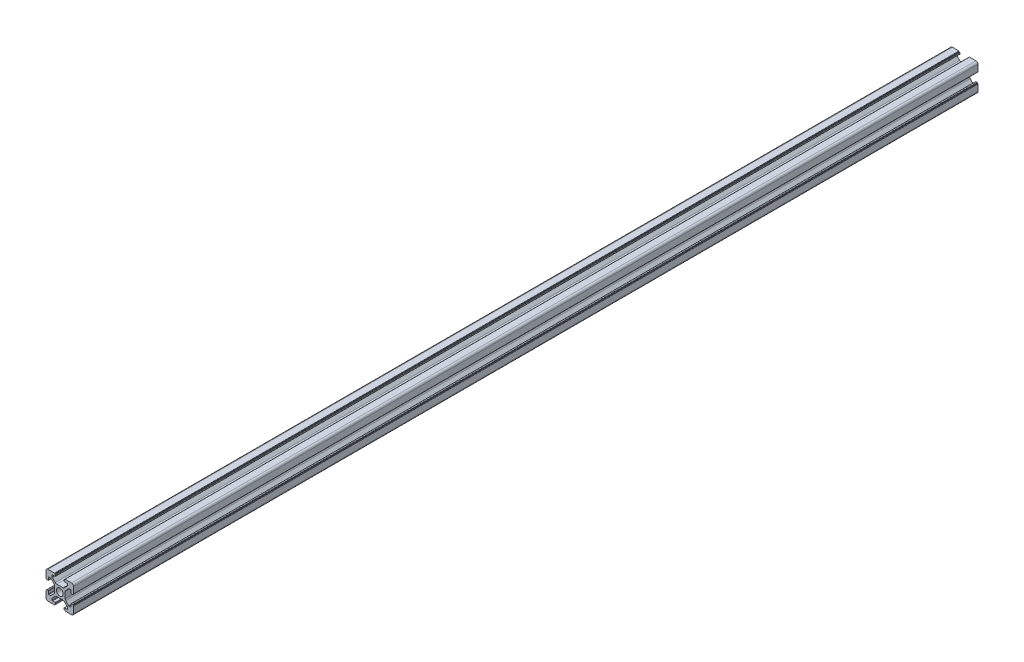
SolidWorks part; units mm, degrees
ref_plane "前视基准面" through (0, 0, 0) normal (0, 0, 1) x (1, 0, 0)
ref_plane "上视基准面" through (0, 0, 0) normal (0, 1, 0) x (1, 0, 0)
ref_plane "右视基准面" through (0, 0, 0) normal (1, 0, 0) x (0, 0, -1)
sketch "草图1" plane through (0, 0, 0) normal (0, 0, 1) x (1, 0, 0)
  line L0 (0, 0) -> (0, 5.5) construction
  line L1 (-8.5023, -10.0023) -> (-3.85, -10.0023)
  line L2 (-10.0023, -8.5023) -> (-10.0023, -3.85)
  line L3 (-8.5023, 10.0023) -> (-3.85, 10.0023)
  line L4 (10.0023, -8.5023) -> (10.0023, -3.85)
  line L5 (-10.0023, -10.0023) -> (10.0023, 10.0023) construction
  line L6 (-10.0023, 10.0023) -> (10.0023, -10.0023) construction
  line L7 (-2.218, -3.9) -> (2.218, -3.9)
  line L8 (-3.9, -2.218) -> (-3.9, 2.218)
  line L9 (-2.218, 3.9) -> (2.218, 3.9)
  line L10 (3.9, -2.218) -> (3.9, 2.218)
  line L11 (-3.9, -3.9) -> (3.9, 3.9) construction
  line L12 (-3.9, 3.9) -> (3.9, -3.9) construction
  line L13 (-5.25, -8.2) -> (-3.35, -8.2)
  line L14 (-8.2, -5.25) -> (-8.2, -3.35)
  line L15 (-5.25, 8.2) -> (-3.35, 8.2)
  line L16 (8.2, -5.25) -> (8.2, -3.35)
  line L17 (-8.2, -8.2) -> (8.2, 8.2) construction
  line L18 (-8.2, 8.2) -> (8.2, -8.2) construction
  line L19 (-7.95, 5.5) -> (-6.6642, 5.5)
  line L20 (0, 0) -> (5.5, 0) construction
  line L23 (-5.5, 7.95) -> (-5.5, 6.6642)
  line L26 (0, 0) -> (-0.5303, 0.5303)
  line L27 (3.2787, 4.3393) -> (5.4268, 6.4874)
  line L28 (0, 0) -> (0.5303, -0.5303)
  line L29 (5.5, 6.6642) -> (5.5, 7.95)
  line L30 (4.3393, 3.2787) -> (6.4874, 5.4268)
  line L31 (6.6642, 5.5) -> (7.95, 5.5)
  line L32 (4.3393, -3.2787) -> (6.4874, -5.4268)
  line L33 (3.2787, -4.3393) -> (5.4268, -6.4874)
  line L34 (-3.2787, -4.3393) -> (-5.4268, -6.4874)
  line L35 (-4.3393, -3.2787) -> (-6.4874, -5.4268)
  line L36 (-4.3393, 3.2787) -> (-6.4874, 5.4268)
  line L37 (-3.2787, 4.3393) -> (-5.4268, 6.4874)
  line L38 (3.1, -8.45) -> (3.1, -9.2523)
  line L39 (8.45, 3.1) -> (9.2523, 3.1)
  line L40 (-5.5, -6.6642) -> (-5.5, -7.95)
  line L41 (-6.6642, -5.5) -> (-7.95, -5.5)
  line L42 (5.5, -6.6642) -> (5.5, -7.95)
  line L43 (6.6642, -5.5) -> (7.95, -5.5)
  line L44 (9.2523, -3.1) -> (8.45, -3.1)
  line L46 (10.0023, 3.85) -> (10.0023, 8.5023)
  line L47 (8.2, 3.35) -> (8.2, 5.25)
  line L48 (-3.1, -9.2523) -> (-3.1, -8.45)
  line L49 (-8.45, -3.1) -> (-9.2523, -3.1)
  line L50 (-9.2523, 3.1) -> (-8.45, 3.1)
  line L51 (-3.1, 8.45) -> (-3.1, 9.2523)
  line L52 (3.1, 9.2523) -> (3.1, 8.45)
  line L53 (3.85, 10.0023) -> (8.5023, 10.0023)
  line L54 (3.35, 8.2) -> (5.25, 8.2)
  line L55 (-10.0023, 3.85) -> (-10.0023, 8.5023)
  line L56 (-8.2, 3.35) -> (-8.2, 5.25)
  line L57 (3.35, -8.2) -> (5.25, -8.2)
  line L58 (3.85, -10.0023) -> (8.5023, -10.0023)
  line L59 (9.7523, -3.6) -> (9.5023, -3.6)
  line L61 (9.7523, 3.6) -> (9.5023, 3.6)
  line L62 (9.5023, -3.6) -> (9.5023, -3.35)
  line L63 (3.6, -9.7523) -> (3.6, -9.5023)
  line L64 (3.35, -9.5023) -> (3.6, -9.5023)
  line L65 (9.5023, 3.35) -> (9.5023, 3.6)
  line L66 (-3.6, -9.5023) -> (-3.35, -9.5023)
  line L67 (-3.6, -9.7523) -> (-3.6, -9.5023)
  line L68 (-9.7523, -3.6) -> (-9.5023, -3.6)
  line L69 (-9.5023, -3.35) -> (-9.5023, -3.6)
  line L70 (-9.5023, 3.6) -> (-9.5023, 3.35)
  line L71 (-9.7523, 3.6) -> (-9.5023, 3.6)
  line L72 (-3.6, 9.7523) -> (-3.6, 9.5023)
  line L73 (-3.35, 9.5023) -> (-3.6, 9.5023)
  line L74 (3.6, 9.5023) -> (3.35, 9.5023)
  line L75 (3.6, 9.7523) -> (3.6, 9.5023)
  circle A0 centre (0, 0) radius 2.5
  arc A1 (10.0023, 8.5023) -> (8.5023, 10.0023) centre (8.5023, 8.5023) ccw
  arc A2 (8.5023, -10.0023) -> (10.0023, -8.5023) centre (8.5023, -8.5023) ccw
  arc A3 (-10.0023, -8.5023) -> (-8.5023, -10.0023) centre (-8.5023, -8.5023) ccw
  arc A4 (-10.0023, 8.5023) -> (-8.5023, 10.0023) centre (-8.5023, 8.5023) cw
  arc A5 (-9.5023, -3.35) -> (-9.2523, -3.1) centre (-9.2523, -3.35) cw
  arc A6 (-9.7523, -3.6) -> (-10.0023, -3.85) centre (-9.7523, -3.85) ccw
  arc A7 (-8.45, -3.1) -> (-8.2, -3.35) centre (-8.45, -3.35) cw
  arc A8 (-7.95, -5.5) -> (-8.2, -5.25) centre (-7.95, -5.25) cw
  arc A9 (-6.4874, -5.4268) -> (-6.6642, -5.5) centre (-6.6642, -5.25) cw
  arc A10 (-5.4268, -6.4874) -> (-5.5, -6.6642) centre (-5.25, -6.6642) ccw
  arc A11 (-5.5, -7.95) -> (-5.25, -8.2) centre (-5.25, -7.95) ccw
  arc A12 (-3.6, -9.7523) -> (-3.85, -10.0023) centre (-3.85, -9.7523) cw
  arc A13 (-3.35, -9.5023) -> (-3.1, -9.2523) centre (-3.35, -9.2523) ccw
  arc A14 (-3.1, -8.45) -> (-3.35, -8.2) centre (-3.35, -8.45) ccw
  arc A15 (3.1, -8.45) -> (3.35, -8.2) centre (3.35, -8.45) cw
  arc A16 (5.5, -7.95) -> (5.25, -8.2) centre (5.25, -7.95) cw
  arc A17 (5.4268, -6.4874) -> (5.5, -6.6642) centre (5.25, -6.6642) cw
  arc A18 (6.4874, -5.4268) -> (6.6642, -5.5) centre (6.6642, -5.25) ccw
  arc A19 (7.95, -5.5) -> (8.2, -5.25) centre (7.95, -5.25) ccw
  arc A20 (8.45, -3.1) -> (8.2, -3.35) centre (8.45, -3.35) ccw
  arc A21 (9.5023, -3.35) -> (9.2523, -3.1) centre (9.2523, -3.35) ccw
  arc A22 (9.7523, -3.6) -> (10.0023, -3.85) centre (9.7523, -3.85) cw
  arc A23 (3.35, -9.5023) -> (3.1, -9.2523) centre (3.35, -9.2523) cw
  arc A24 (3.6, -9.7523) -> (3.85, -10.0023) centre (3.85, -9.7523) ccw
  arc A25 (7.95, 5.5) -> (8.2, 5.25) centre (7.95, 5.25) cw
  arc A26 (8.2, 3.35) -> (8.45, 3.1) centre (8.45, 3.35) ccw
  arc A27 (9.5023, 3.35) -> (9.2523, 3.1) centre (9.2523, 3.35) cw
  arc A28 (9.7523, 3.6) -> (10.0023, 3.85) centre (9.7523, 3.85) ccw
  arc A29 (6.6642, 5.5) -> (6.4874, 5.4268) centre (6.6642, 5.25) ccw
  arc A30 (5.4268, 6.4874) -> (5.5, 6.6642) centre (5.25, 6.6642) ccw
  arc A31 (5.5, 7.95) -> (5.25, 8.2) centre (5.25, 7.95) ccw
  arc A32 (3.1, 8.45) -> (3.35, 8.2) centre (3.35, 8.45) ccw
  arc A33 (3.6, 9.7523) -> (3.85, 10.0023) centre (3.85, 9.7523) cw
  arc A34 (3.35, 9.5023) -> (3.1, 9.2523) centre (3.35, 9.2523) ccw
  arc A35 (-9.7523, 3.6) -> (-10.0023, 3.85) centre (-9.7523, 3.85) cw
  arc A36 (-9.5023, 3.35) -> (-9.2523, 3.1) centre (-9.2523, 3.35) ccw
  arc A37 (-8.45, 3.1) -> (-8.2, 3.35) centre (-8.45, 3.35) ccw
  arc A38 (-8.2, 5.25) -> (-7.95, 5.5) centre (-7.95, 5.25) cw
  arc A39 (-6.4874, 5.4268) -> (-6.6642, 5.5) centre (-6.6642, 5.25) ccw
  arc A40 (-5.4268, 6.4874) -> (-5.5, 6.6642) centre (-5.25, 6.6642) cw
  arc A41 (-5.5, 7.95) -> (-5.25, 8.2) centre (-5.25, 7.95) cw
  arc A42 (-3.1, 8.45) -> (-3.35, 8.2) centre (-3.35, 8.45) cw
  arc A43 (-3.1, 9.2523) -> (-3.35, 9.5023) centre (-3.35, 9.2523) ccw
  arc A44 (-3.6, 9.7523) -> (-3.85, 10.0023) centre (-3.85, 9.7523) ccw
  arc A45 (-4.3393, 3.2787) -> (-3.9, 2.218) centre (-5.4, 2.218) cw
  arc A46 (-3.2787, 4.3393) -> (-2.218, 3.9) centre (-2.218, 5.4) ccw
  arc A47 (3.2787, 4.3393) -> (2.218, 3.9) centre (2.218, 5.4) cw
  arc A48 (4.3393, 3.2787) -> (3.9, 2.218) centre (5.4, 2.218) ccw
  arc A49 (4.3393, -3.2787) -> (3.9, -2.218) centre (5.4, -2.218) cw
  arc A50 (3.2787, -4.3393) -> (2.218, -3.9) centre (2.218, -5.4) ccw
  arc A51 (-4.3393, -3.2787) -> (-3.9, -2.218) centre (-5.4, -2.218) ccw
  arc A52 (-2.218, -3.9) -> (-3.2787, -4.3393) centre (-2.218, -5.4) ccw
  point P0 (0, 0)
  point P7 (10.0023, 0)
  point P62 (0, 0)
  point P76 (0, 0)
  point P92 (-8.2, -5.5)
  point P99 (0, 0)
  point P106 (-5.5, -8.2)
  point P117 (5.5, -8.2)
  point P124 (8.2, -5.5)
  point P137 (8.2, 5.5)
  point P140 (8.2, 3.1)
  point P147 (6.5607, 5.5)
  point P152 (5.5, 8.2)
  point P167 (-8.2, 5.5)
  point P174 (-5.5, 8.2)
  dimension "D1" = 1.5
  dimension "D5" = 0.25
  dimension "D6" = 1.5
  dimension "D2" = 4
  dimension "D3" = 4
  dimension "D4" = 4
extrude "凸台-拉伸1" add sketch "草图1" along normal blind 1220 contours A52 L7 A50 L33 A17 L42 A16 L57 A15 L38 A23 L64 L63 A24 L58 A2 L4 A22 L59 L62 A21 L44 A20 L16 A19 L43 A18 L32 A49 L10 A48 L30 A29 L31 A25 L47 A26 L39 A27 L65 L61 A28 L46 A1 L53 A33 L75 L74 A34 L52 A32
ref_plane "Plane1" through (0, 0, 564) normal (0, 0, 1) x (1, 0, 0)
sketch "Sketch1" plane through (0, 0, 564) normal (0, 0, 1) x (1, 0, 0)
  circle A0 centre (0, 0) radius 16.7715
extrude "Cut-Extrude1" cut sketch "Sketch1" against normal through all
ref_plane "CenterPlane" through (0, 0, 892) normal (0, 0, 1) x (1, 0, 0)
